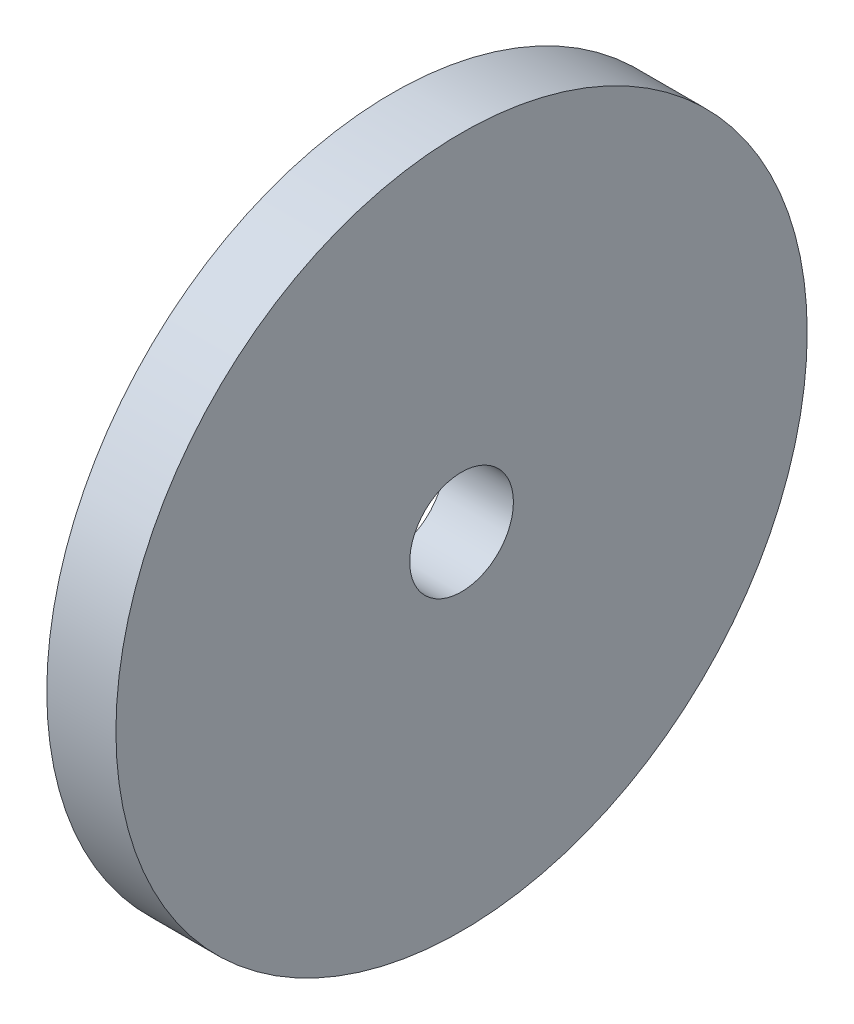
SolidWorks part; units mm, degrees
material "Pine"
ref_plane "Front Plane" through (0, 0, 0) normal (0, 0, 1) x (1, 0, 0)
ref_plane "Top Plane" through (0, 0, 0) normal (0, 1, 0) x (1, 0, 0)
ref_plane "Right Plane" through (0, 0, 0) normal (1, 0, 0) x (0, 0, -1)
sketch "Sketch1" plane through (0, 0, 0) normal (1, 0, 0) x (0, 0, -1)
  circle A0 centre (0, 0) radius 10
  dimension "D1" = 20
extrude "Boss-Extrude1" add sketch "Sketch1" along normal blind 2
sketch "Sketch2" plane through (2, 0, 0) normal (1, 0, 0) x (0, 0, -1)
  circle A1 centre (0, 0) radius 1.5
extrude "Cut-Extrude1" cut sketch "Sketch2" against normal through all
